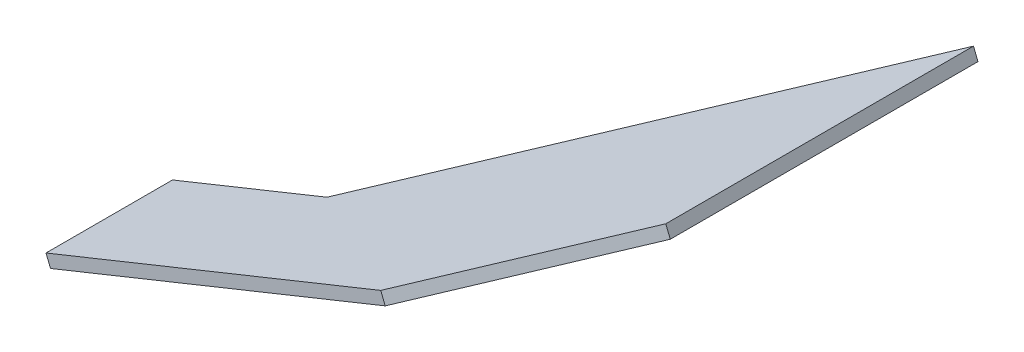
SolidWorks part; units mm, degrees
ref_plane "Front Plane" through (0, 0, 0) normal (0, 0, 1) x (1, 0, 0)
ref_plane "Top Plane" through (0, 0, 0) normal (0, 1, 0) x (1, 0, 0)
ref_plane "Right Plane" through (0, 0, 0) normal (1, 0, 0) x (0, 0, -1)
ref_plane "Plane1" through (45.8907, -113.8199, 0) normal (0.3739, -0.9275, 0) x (0.9275, 0.3739, 0)
sketch "Sketch2" plane through (45.8907, -113.8199, 0) normal (0.3739, -0.9275, 0) x (0.9275, 0.3739, 0)
  line L0 (7030.7294, -5519.062) -> (7030.7294, -5550.5528)
  line L2 (7030.7294, -5550.5528) -> (7072.194, -5550.5528)
  line L4 (7072.194, -5550.5528) -> (7158.7294, -5631.2483)
  line L5 (7158.7294, -5631.2483) -> (7158.7294, -5554.6426)
  line L6 (7158.7294, -5554.6426) -> (7120.5739, -5519.062)
  line L8 (7120.5739, -5519.062) -> (7030.7294, -5519.062)
  line L9 (7030.7294, -5519.062) -> (7095.2547, -5519.062) construction
  line L10 (7072.194, -5550.5528) -> (7030.7294, -5550.5528) construction
  line L11 (7030.7294, -5550.5528) -> (7030.7294, -5553.5528) construction
  line L12 (7120.5739, -5519.062) -> (7155.7294, -5551.845) construction
  line L14 (7072.194, -5550.5528) -> (7158.7294, -5631.2483) construction
  line L15 (7158.7294, -5635.3503) -> (7158.7294, -5631.2483) construction
extrude "Boss-Extrude1" add sketch "Sketch2" along normal blind 3
